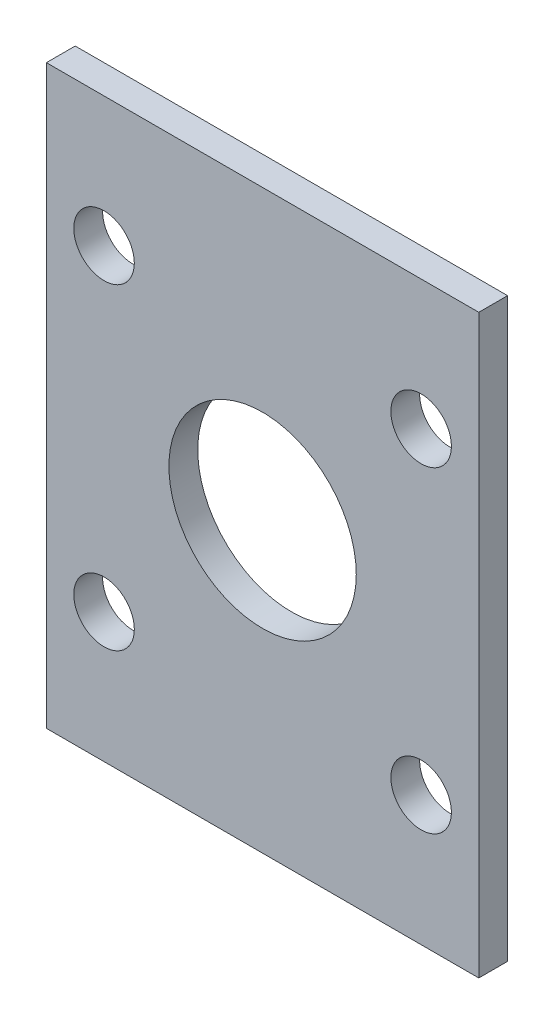
SolidWorks part; units mm, degrees
ref_plane "正面" through (0, 0, 0) normal (0, 0, 1) x (1, 0, 0)
ref_plane "平面" through (0, 0, 0) normal (0, 1, 0) x (1, 0, 0)
ref_plane "右側面" through (0, 0, 0) normal (1, 0, 0) x (0, 0, -1)
sketch "ｽｹｯﾁ1" plane through (0, 0, 0) normal (0, 0, 1) x (1, 0, 0)
  line L1 (-15, 15) -> (15, 15)
  line L2 (-15, 15) -> (-15, -15)
  line L3 (-15, -15) -> (15, -15)
  line L4 (15, 15) -> (15, -15)
  line L5 (-15, 15) -> (15, -15) construction
  line L6 (-15, -15) -> (15, 15) construction
  line L7 (-15, 15) -> (-11, 15)
  line L8 (-15, 15) -> (-15, 11)
  line L9 (-15, 11) -> (-11, 11)
  line L10 (-11, 15) -> (-11, 11)
  line L11 (15, 15) -> (11, 15)
  line L12 (15, 15) -> (15, 11)
  line L13 (15, 11) -> (11, 11)
  line L14 (11, 15) -> (11, 11)
  line L15 (15, -15) -> (11, -15)
  line L16 (15, -15) -> (15, -11)
  line L17 (15, -11) -> (11, -11)
  line L18 (11, -15) -> (11, -11)
  line L19 (-15, -15) -> (-11, -15)
  line L20 (-15, -15) -> (-15, -11)
  line L21 (-15, -11) -> (-11, -11)
  line L22 (-11, -15) -> (-11, -11)
  circle A0 centre (-11, 11) radius 2.1
  circle A1 centre (11, 11) radius 2.1
  circle A2 centre (11, -11) radius 2.1
  circle A3 centre (-11, -11) radius 2.1
  point P1 (0, 0)
  dimension "D11" = 4.2
  dimension "D12" = 4.2
  dimension "D13" = 4.2
  dimension "D14" = 4.2
  dimension "D1" = 30
  dimension "D2" = 30
  dimension "D3" = 4
  dimension "D4" = 4
  dimension "D5" = 4
  dimension "D6" = 4
  dimension "D7" = 4
  dimension "D8" = 4
  dimension "D9" = 4
  dimension "D10" = 4
extrude "ﾎﾞｽ - 押し出し1" add sketch "ｽｹｯﾁ1" along normal blind 2 contours A3 L22 L3 L18 A2 L17 L4 L13 A1 L14 L1 L10 A0 L9 L2 L21 | A2 L18 L3 L4 L17 | A3 L21 L2 L3 L22 | A0 L10 L1 L2 L9 | A1 L13 L4 L1 L14
sketch "ｽｹｯﾁ2" plane through (0, 0, 2) normal (0, 0, 1) x (1, 0, 0)
  circle A0 centre (0, 0) radius 6.5
  dimension "D1" = 13
extrude "ｶｯﾄ - 押し出し1" cut sketch "ｽｹｯﾁ2" against normal blind 2
sketch "ｽｹｯﾁ3" plane through (15, 0, 0) normal (1, 0, 0) x (0, 0, -1)
  line L1 (-2, -15) -> (0, -15)
  line L2 (-2, -15) -> (-2, 15)
  line L3 (-2, 15) -> (0, 15)
  line L4 (0, -15) -> (0, 15)
sketch "ｽｹｯﾁ4" plane through (-15, 0, 0) normal (-1, 0, 0) x (0, 0, 1)
  line L1 (2, 15) -> (0, 15)
  line L2 (2, 15) -> (2, -15)
  line L3 (2, -15) -> (0, -15)
  line L4 (0, 15) -> (0, -15)
sketch "ｽｹｯﾁ5" plane through (0, 15, 0) normal (0, 1, 0) x (1, 0, 0)
  line L1 (-15, 0) -> (15, 0)
  line L2 (-15, 0) -> (-15, -2)
  line L3 (-15, -2) -> (15, -2)
  line L4 (15, 0) -> (15, -2)
extrude "ﾎﾞｽ - 押し出し4" add sketch "ｽｹｯﾁ5" along normal blind 5
sketch "ｽｹｯﾁ6" plane through (0, -15, 0) normal (0, -1, 0) x (-1, 0, 0)
  line L1 (15, 0) -> (-15, 0)
  line L2 (15, 0) -> (15, -2)
  line L3 (15, -2) -> (-15, -2)
  line L4 (-15, 0) -> (-15, -2)
extrude "ﾎﾞｽ - 押し出し5" add sketch "ｽｹｯﾁ6" along normal blind 5
